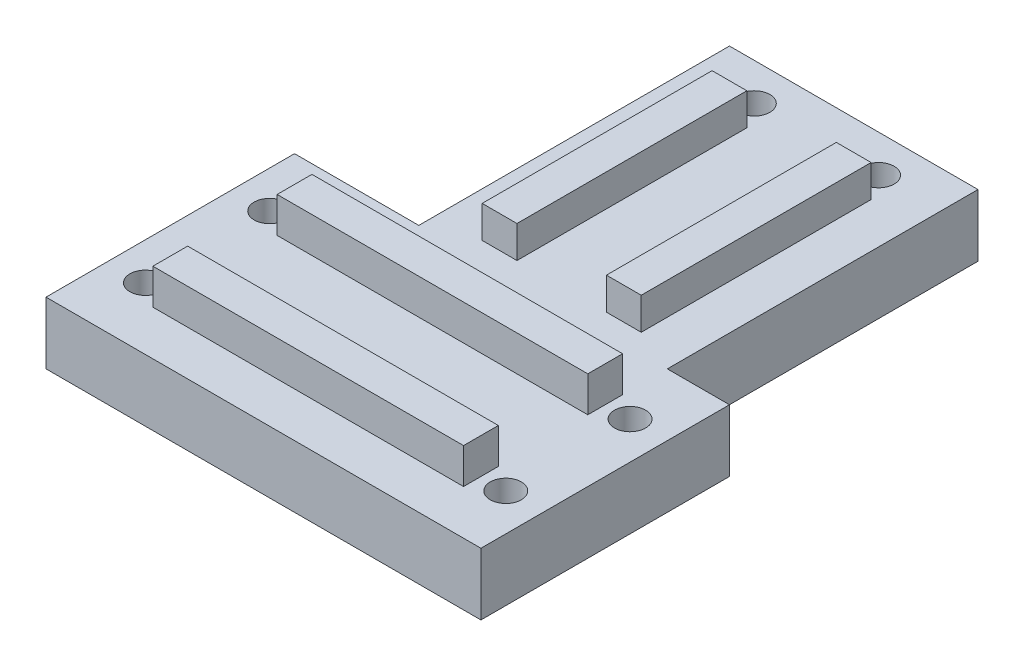
SolidWorks part; units mm, degrees
ref_plane "Alzado" through (0, 0, 0) normal (0, 0, 1) x (1, 0, 0)
ref_plane "Planta" through (0, 0, 0) normal (0, 1, 0) x (1, 0, 0)
ref_plane "Vista lateral" through (0, 0, 0) normal (1, 0, 0) x (0, 0, -1)
sketch "Croquis1" plane through (0, 0, 0) normal (0, 1, 0) x (1, 0, 0)
  line L1 (30, 20) -> (-30, 20)
  line L2 (30, 20) -> (30, -20)
  line L3 (30, -20) -> (-30, -20)
  line L7 (-30, -20) -> (-70, -20)
  line L9 (-30, 20) -> (-70, 20)
  line L10 (-70, -20) -> (-70, 20)
  point P0 (0, 0)
  dimension "D1" = 40
  dimension "D2" = 60
  dimension "D3" = 40
extrude "Saliente-Extruir1" add sketch "Croquis1" along normal blind 10
sketch "Croquis3" plane through (-70, 0, 0) normal (-1, 0, 0) x (0, 0, 1)
  line L0 (-20, 10) -> (20, 10) construction
  line L16 (20, 10) -> (20, 0) construction
  line B0 (10, 15.7111) -> (10, 7.529) construction
  line B1 (10, 10) -> (7.2, 10)
  line B2 (12.8, 10) -> (10, 10)
  line B3 (7.2, 10) -> (7.2, 15.7111)
  line B4 (12.8, 15.7111) -> (12.8, 10)
  line B5 (7.2, 15.7111) -> (12.8, 15.7111)
  line B6 (-10, 15.7111) -> (-10, 7.529) construction
  line B7 (-10, 10) -> (-12.8, 10)
  line B8 (-7.2, 10) -> (-10, 10)
  line B9 (-12.8, 10) -> (-12.8, 15.7111)
  line B10 (-7.2, 15.7111) -> (-7.2, 10)
  line B11 (-12.8, 15.7111) -> (-7.2, 15.7111)
  dimension "D1" = 10
  dimension "D2" = 2
  dimension "D3" = 20
sketch_block_instance "Bloque1-1"
sketch_block "Bloque1" parameters "D1"=1.5, "D2"=8.1821
sketch_block_instance "Bloque1-2"
extrude "Saliente-Extruir3" add sketch "Croquis3" against normal through all
sketch "Croquis5" plane through (0, 10, 0) normal (0, 1, 0) x (1, 0, 0)
  line L1 (-20, 70) -> (20, 70)
  line L2 (-20, 70) -> (-20, 20)
  line L3 (-20, 20) -> (20, 20)
  line L4 (20, 70) -> (20, 20)
  line L6 (30, 20) -> (-70, 20) construction
  dimension "D1" = 50
  dimension "D2" = 40
  dimension "D3" = 50
extrude "Saliente-Extruir5" add sketch "Croquis5" against normal blind 10
sketch "Croquis7" plane through (0, 0, -70) normal (0, 0, -1) x (-1, 0, 0)
  line L0 (-20, 10) -> (20, 10) construction
  line L25 (20, 0) -> (20, 10) construction
  line B0 (10, 15.1656) -> (10, 5.7209) construction
  line B1 (12.8, 10) -> (10, 10)
  line B2 (7.2, 10) -> (7.2, 15.1656)
  line B3 (12.8, 15.1656) -> (12.8, 10)
  line B4 (10, 10) -> (7.2, 10)
  line B5 (7.2, 15.1656) -> (12.8, 15.1656)
  line B6 (-10, 15.1656) -> (-10, 5.7209) construction
  line B7 (-7.2, 10) -> (-10, 10)
  line B8 (-12.8, 10) -> (-12.8, 15.1656)
  line B9 (-7.2, 15.1656) -> (-7.2, 10)
  line B10 (-10, 10) -> (-12.8, 10)
  line B11 (-12.8, 15.1656) -> (-7.2, 15.1656)
  dimension "D1" = 10
  dimension "D2" = 2
  dimension "D3" = 20
sketch_block_instance "Bloque2-1"
sketch_block "Bloque2" parameters "D1"=1.5, "D2"=1.5
sketch_block_instance "Bloque2-2"
extrude "Saliente-Extruir7" add sketch "Croquis7" against normal blind 47
sketch "Croquis11" plane through (-70, 0, 0) normal (-1, 0, 0) x (0, 0, 1)
  line L1 (37.0483, -81.1224) -> (-37.0483, -81.1224)
  line L2 (37.0483, -81.1224) -> (37.0483, 81.1224)
  line L3 (37.0483, 81.1224) -> (-37.0483, 81.1224)
  line L4 (-37.0483, -81.1224) -> (-37.0483, 81.1224)
  line L5 (37.0483, -81.1224) -> (-37.0483, 81.1224) construction
  line L6 (37.0483, 81.1224) -> (-37.0483, -81.1224) construction
extrude "Cortar-Extruir3" cut sketch "Croquis11" against normal blind 30
sketch "Croquis9" plane through (0, 10, 0) normal (0, 1, 0) x (1, 0, 0)
  line L1 (30, 20) -> (20, 20)
  line L2 (30, 20) -> (30, -20)
  line L3 (30, -20) -> (20, -20)
  line L4 (20, 20) -> (20, -20)
  line L5 (-40, -20) -> (30, -20) construction
  line L6 (30, 20) -> (20, 20) construction
  line L8 (20, 70) -> (-20, 70)
  line L9 (20, 70) -> (20, 60)
  line L10 (20, 60) -> (-20, 60)
  line L11 (-20, 70) -> (-20, 60)
  line L12 (-20, 70) -> (-20, 20) construction
  line L13 (20, 20) -> (20, 70) construction
  line L31 (30, -7.2) -> (30, 7.2) construction
  line L32 (7.2, 70) -> (-7.2, 70) construction
  line L33 (-40, -20) -> (30, -20) construction
  line L34 (-40, -20) -> (-30, -20)
  line L35 (-40, -20) -> (-40, 20)
  line L36 (-40, 20) -> (-30, 20)
  line L37 (-30, -20) -> (-30, 20)
  line L38 (-40, -20) -> (-30, 20) construction
  line L39 (-40, 20) -> (-30, -20) construction
  line L40 (-20, 20) -> (-40, 20) construction
  line L41 (-40, -7.2) -> (-40, 7.2) construction
  point P20 (-35, 0)
  dimension "D1" = 10
  dimension "D2" = 10
  dimension "D4" = 10
extrude "Cortar-Extruir1" cut sketch "Croquis9" along direction (0, 1, 0) on the side of the normal through all
sketch "Croquis12" plane through (0, 10, 0) normal (0, 1, 0) x (1, 0, 0)
  line L1 (-40, -20) -> (30, -20) construction
  line L2 (20, 20) -> (20, 70) construction
  line L3 (30, -20) -> (30, 20) construction
  line L4 (20, 70) -> (-20, 70) construction
  line L5 (-40, -20) -> (-40, 20) construction
  circle A0 centre (24, -10) radius 2.5
  circle A1 centre (24, 10) radius 2.5
  circle A2 centre (-34, -10) radius 2.5
  circle A3 centre (-34, 10) radius 2.5
  circle A4 centre (10, 64) radius 2.5
  circle A5 centre (-10, 64) radius 2.5
  dimension "D1" = 5
  dimension "D2" = 10
  dimension "D3" = 20
  dimension "D4" = 10
  dimension "D5" = 20
  dimension "D6" = 6
  dimension "D7" = 6
  dimension "D8" = 6
extrude "Cortar-Extruir4" cut sketch "Croquis12" against normal through all
